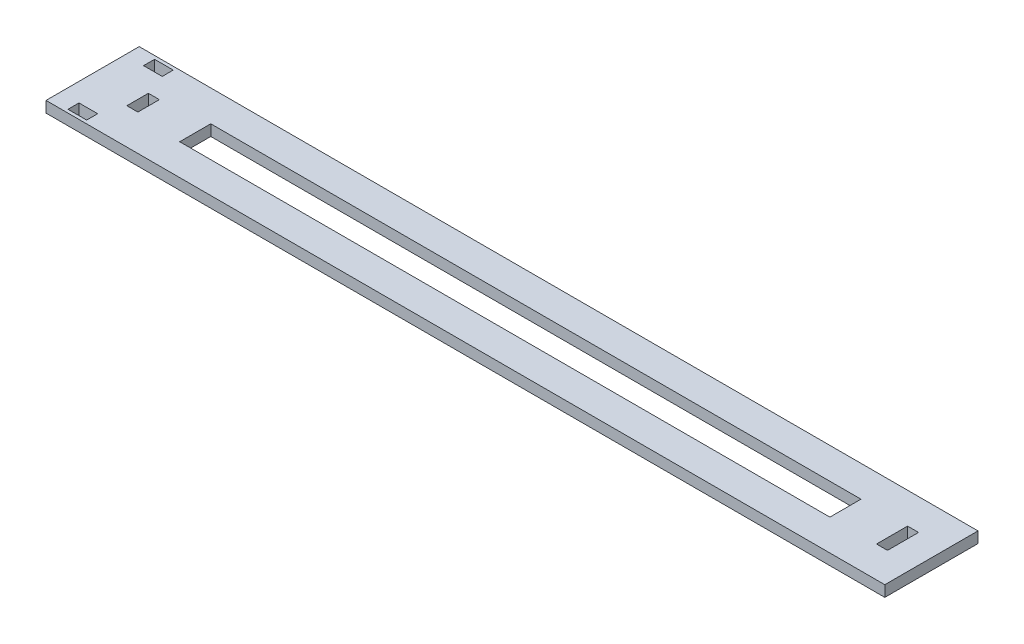
SolidWorks part; units mm, degrees
ref_plane "Front" through (0, 0, 0) normal (0, 0, 1) x (1, 0, 0)
ref_plane "Top" through (0, 0, 0) normal (0, 1, 0) x (1, 0, 0)
ref_plane "Right" through (0, 0, 0) normal (1, 0, 0) x (0, 0, -1)
sketch "Sketch2" plane through (0, 0, 0) normal (0, 1, 0) x (1, 0, 0)
  line L1 (0, 0) -> (457.2, 0)
  line L2 (0, 0) -> (0, 50.8)
  line L3 (0, 50.8) -> (457.2, 50.8)
  line L4 (457.2, 0) -> (457.2, 50.8)
  dimension "D1" = 457.2
  dimension "D2" = 50.8
extrude "Base" add sketch "Sketch2" along normal blind 6
sketch "Sketch3" plane through (0, 6, 0) normal (0, 1, 0) x (1, 0, 0)
  line L0 (457.2, 0) -> (457.2, 50.8) construction
  line L1 (441.74, 33.8667) -> (435.74, 33.8667)
  line L2 (441.74, 33.8667) -> (441.74, 16.9333)
  line L3 (441.74, 16.9333) -> (435.74, 16.9333)
  line L4 (435.74, 33.8667) -> (435.74, 16.9333)
  line L5 (0, 0) -> (457.2, 0) construction
  line L6 (0, 50.8) -> (0, 0) construction
  line L7 (24.54, 31.2667) -> (30.54, 31.2667)
  line L8 (24.54, 31.2667) -> (24.54, 19.5333)
  line L9 (24.54, 19.5333) -> (30.54, 19.5333)
  line L10 (30.54, 31.2667) -> (30.54, 19.5333)
  point P14 (24.54, 25.4)
  point P15 (0, 25.4)
  dimension "D1" = 15.46
  dimension "D2" = 6
  dimension "D3" = 16.9333
  dimension "D4" = 16.9333
  dimension "D5" = 6
  dimension "D6" = 11.7333
  dimension "D7" = 24.54
  dimension "D8" = 0
extrude "Cut-Extrude1" cut sketch "Sketch3" against normal up to next
sketch "Sketch4" plane through (0, 6, 0) normal (0, 1, 0) x (1, 0, 0)
  line L1 (10.18, 7.8) -> (20.36, 7.8)
  line L2 (10.18, 7.8) -> (10.18, 1.8)
  line L3 (10.18, 1.8) -> (20.36, 1.8)
  line L4 (20.36, 7.8) -> (20.36, 1.8)
  line L5 (0, 50.8) -> (0, 0) construction
  line L8 (10.18, 49) -> (20.36, 49)
  line L9 (10.18, 49) -> (10.18, 43)
  line L10 (10.18, 43) -> (20.36, 43)
  line L11 (20.36, 49) -> (20.36, 43)
  line L12 (457.2, 50.8) -> (0, 50.8) construction
  line L13 (0, 0) -> (457.2, 0) construction
  dimension "D1" = 7.8
  dimension "D2" = 10.18
  dimension "D3" = 10.18
  dimension "D4" = 7.8
  dimension "D5" = 10.18
  dimension "D6" = 10.18
  dimension "D7" = 6
  dimension "D8" = 6
extrude "Cut-Extrude2" cut sketch "Sketch4" against normal up to next
sketch "Sketch5" plane through (0, 6, 0) normal (0, 1, 0) x (1, 0, 0)
  line L0 (0, 25.4) -> (457.2, 25.4) construction
  line L1 (0, 50.8) -> (0, 0) construction
  line L2 (457.2, 0) -> (457.2, 50.8) construction
  line L4 (214.8947, 33.8667) -> (242.3053, 33.8667)
  line L5 (242.3053, 33.8667) -> (410.34, 33.8667)
  line L6 (214.8947, 16.9333) -> (242.3053, 16.9333)
  line L7 (410.34, 33.8667) -> (410.34, 16.9333)
  line L8 (214.8947, 33.8667) -> (242.3053, 16.9333) construction
  line L9 (214.8947, 16.9333) -> (242.3053, 33.8667) construction
  line L10 (410.34, 16.9333) -> (242.3053, 16.9333)
  line L11 (214.8947, 16.9333) -> (55.94, 16.9333)
  line L12 (55.94, 16.9333) -> (55.94, 33.8667)
  line L13 (55.94, 33.8667) -> (214.8947, 33.8667)
  line L14 (30.54, 19.5333) -> (30.54, 31.2667) construction
  line L15 (435.74, 33.8667) -> (435.74, 16.9333) construction
  point P6 (228.6, 25.4)
  point P11 (228.6, 25.4)
  point P18 (55.94, 25.4)
  dimension "D1" = 25.4
  dimension "D2" = 0
  dimension "D3" = 25.4
  dimension "D4" = 16.9333
extrude "Cut-Extrude3" cut sketch "Sketch5" against normal up to next
